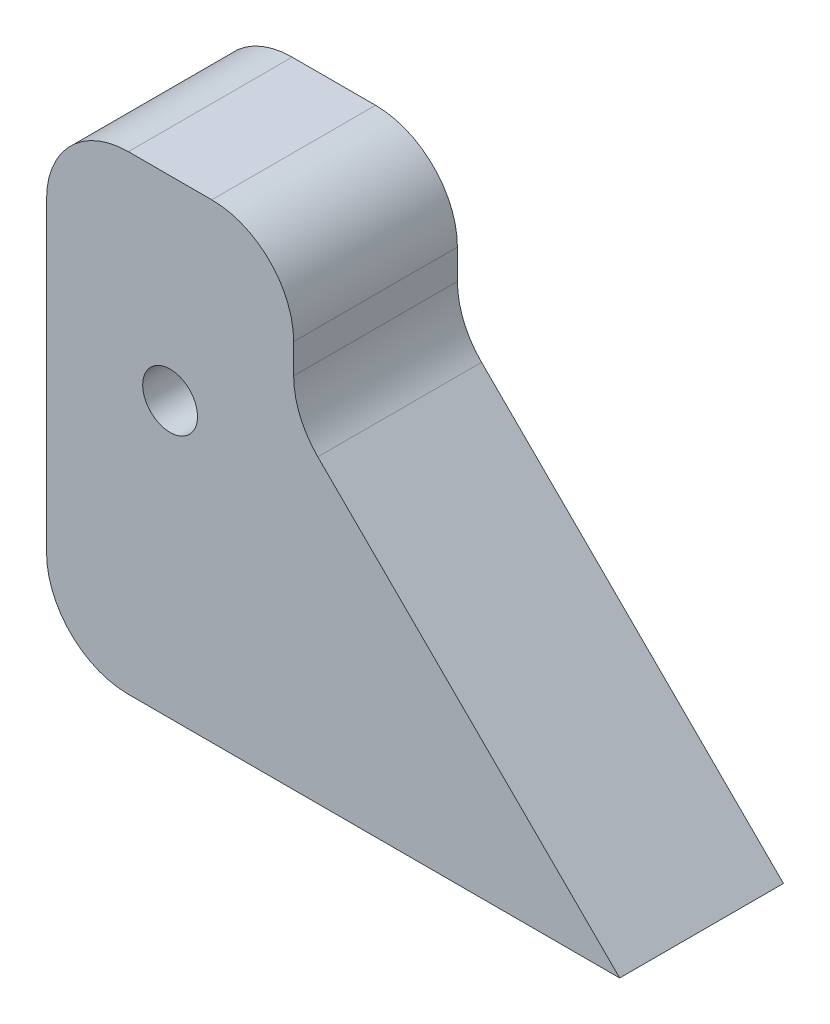
SolidWorks part; units mm, degrees
ref_plane "Front Plane" through (0, 0, 0) normal (0, 0, 1) x (1, 0, 0)
ref_plane "Top Plane" through (0, 0, 0) normal (0, 1, 0) x (1, 0, 0)
ref_plane "Right Plane" through (0, 0, 0) normal (1, 0, 0) x (0, 0, -1)
sketch "Sketch1" plane through (0, 0, 0) normal (0, 0, 1) x (1, 0, 0)
  line L1 (0, 0) -> (35, 0)
  line L2 (0, 0) -> (0, 28.7)
  line L3 (0, 28.7) -> (15.09, 28.7)
  line L4 (15.09, 28.7) -> (15.09, 19.81)
  line L5 (15.09, 19.81) -> (35, 0)
  dimension "D2" = 35
  dimension "D3" = 28.7
  dimension "D4" = 15.09
  dimension "D5" = 8.89
extrude "Boss-Extrude1" add sketch "Sketch1" along normal blind 10
fillet "Fillet1" radius 5 4 edges at (0, 0, 5) (15.09, 19.81, 5) (15.09, 28.7, 5) (0, 28.7, 5)
ref_plane "Plane1" through (0, 0, 10) normal (0, 0, 1) x (1, 0, 0)
sketch "Sketch2" plane through (0, 0, 10) normal (0, 0, 1) x (1, 0, 0)
  line L3 (7.545, 0) -> (7.545, 16.8)
  line L4 (5, 0) -> (35, 0) construction
  circle A0 centre (7.545, 16.8) radius 3.2
  dimension "D2" = 6.4
  dimension "D1" = 16.8
extrude "Cut-Extrude1" cut sketch "Sketch2" against normal blind 4.7
sketch "Sketch3" plane through (0, 0, 10) normal (0, 0, 1) x (1, 0, 0)
  circle A0 centre (7.545, 16.8) radius 1.6
  dimension "D1" = 3.2
extrude "Cut-Extrude2" cut sketch "Sketch3" against normal blind 10
ref_plane "Plane2" through (0, 0, 0) normal (0, 0, -1) x (-1, 0, 0)
sketch "Sketch5" plane through (0, 0, 0) normal (0, 0, -1) x (-1, 0, 0)
  circle A0 centre (-7.545, 16.8) radius 3.2
  dimension "D1" = 6.4
extrude "Cut-Extrude3" cut sketch "Sketch5" against normal blind 4.7
sketch "Sketch6" plane through (0, 0, 10) normal (0, 0, 1) x (1, 0, 0)
  circle A0 centre (7.545, 16.8) radius 3.2
extrude "Boss-Extrude2" add sketch "Sketch6" against normal blind 4.7
sketch "Sketch8" plane through (0, 0, 0) normal (0, 0, -1) x (-1, 0, 0)
  circle A0 centre (-7.545, 16.8) radius 1.675
  dimension "D1" = 3.35
extrude "Cut-Extrude4" cut sketch "Sketch8" against normal blind 10
